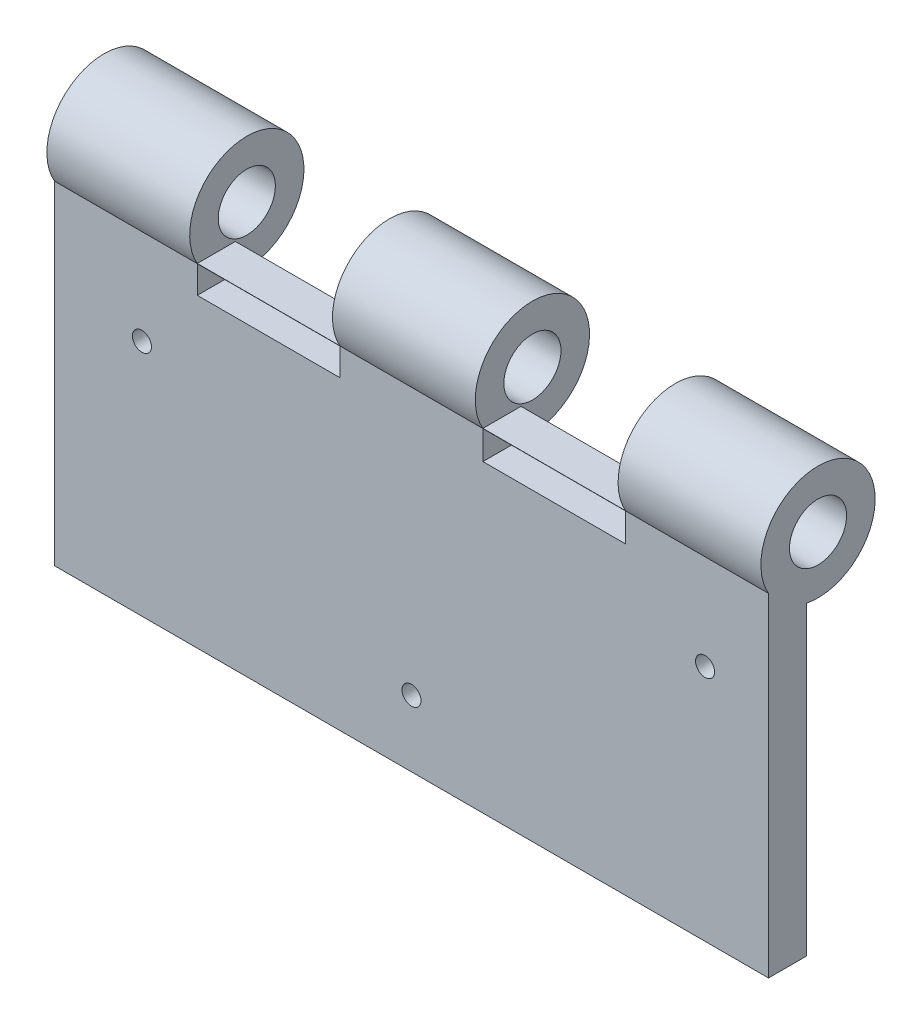
SolidWorks part; units mm, degrees
ref_plane "Front Plane" through (0, 0, 0) normal (0, 0, 1) x (1, 0, 0)
ref_plane "Top Plane" through (0, 0, 0) normal (0, 1, 0) x (1, 0, 0)
ref_plane "Right Plane" through (0, 0, 0) normal (1, 0, 0) x (0, 0, -1)
sketch "Sketch1" plane through (0, 0, 0) normal (0, 0, 1) x (1, 0, 0)
  line L1 (75, -35) -> (-75, -35)
  line L2 (75, -35) -> (75, 35)
  line L3 (75, 35) -> (-75, 35)
  line L4 (-75, -35) -> (-75, 35)
  line L5 (75, -35) -> (-75, 35) construction
  line L6 (75, 35) -> (-75, -35) construction
  point P0 (0, 0)
  dimension "D1" = 70
  dimension "D2" = 150
extrude "Boss-Extrude1" add sketch "Sketch1" along normal mid plane 8
sketch "Sketch4" plane through (75, 0, 0) normal (1, 0, 0) x (0, 0, -1)
  circle A0 centre (6.4004, 40.9538) radius 12
  circle A1 centre (6.4004, 40.9538) radius 6
  dimension "D1" = 24
  dimension "D2" = 12
extrude "Boss-Extrude6" add sketch "Sketch4" against normal blind 30 contours A1 | A0
pattern_linear "LPattern1" count 3 spacing 60 along (-1, 0, 0) of "Boss-Extrude6"
sketch "Sketch7" plane through (0, 0, 4) normal (0, 0, 1) x (1, 0, 0)
  circle A0 centre (-56.6305, 15.0159) radius 2
  circle A1 centre (0, -21.0581) radius 2
  circle A2 centre (61.6697, 15.0159) radius 2
  dimension "D1" = 4
extrude "Cut-Extrude2" cut sketch "Sketch7" against normal blind 30
chamfer "Chamfer3" distance 4 angle 45 3 edges at (-54.6305, 15.0159, -4) (2, -21.0581, -4) (63.6697, 15.0159, -4)
sketch "Sketch8" plane through (0, 0, -4) normal (0, 0, -1) x (-1, 0, 0)
  line L1 (-45, 34.9538) -> (-15, 34.9538)
  line L2 (-45, 34.9538) -> (-45, 28.9538)
  line L3 (-45, 28.9538) -> (-15, 28.9538)
  line L4 (-15, 34.9538) -> (-15, 28.9538)
extrude "Cut-Extrude3" cut sketch "Sketch8" against normal blind 10
sketch "Sketch9" plane through (0, 0, -4) normal (0, 0, -1) x (-1, 0, 0)
  line L1 (15, 34.9538) -> (45, 34.9538)
  line L2 (15, 34.9538) -> (15, 29.1963)
  line L3 (15, 29.1963) -> (45, 29.1963)
  line L4 (45, 34.9538) -> (45, 29.1963)
extrude "Cut-Extrude4" cut sketch "Sketch9" against normal blind 10
